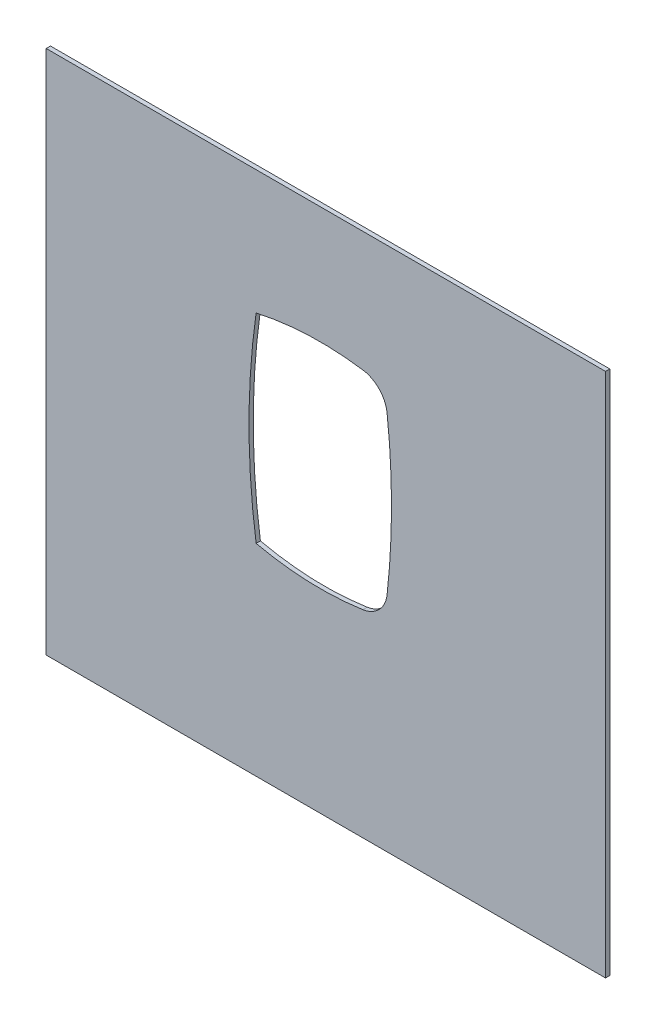
SolidWorks part; units mm, degrees
material "Rostfreier Chromstahl"
ref_plane "Ebene vorne" through (0, 0, 0) normal (0, 0, 1) x (1, 0, 0)
ref_plane "Ebene oben" through (0, 0, 0) normal (0, 1, 0) x (1, 0, 0)
ref_plane "Ebene rechts" through (0, 0, 0) normal (1, 0, 0) x (0, 0, -1)
sketch "Skizze1" plane through (0, 0, 0) normal (0, 0, 1) x (1, 0, 0)
  line L0 (0, -130) -> (0, 130) construction
  line L1 (442.5, 0) -> (-442.5, 0) construction
  line L2 (0, -130) -> (0, 75) construction
  line L4 (-192.2736, 157.0766) -> (200.1363, 157.0766)
  line L5 (-442.5, 0) -> (50, 0) construction
  line L6 (0, 130) -> (0, -75) construction
  line L7 (442.5, 0) -> (-50, 0) construction
  line L8 (-192.2736, 157.0766) -> (-192.2736, -211.5028)
  line L9 (-192.2736, -211.5028) -> (200.1363, -211.5028)
  line L10 (200.1363, 157.0766) -> (200.1363, -211.5028)
  arc A0 (29.9369, 72.8023) -> (-45, 70) centre (0, -130) ccw
  arc A1 (-45, -70) -> (29.9369, -72.8023) centre (0, 130) ccw
  arc A2 (-45, 70) -> (-45, -70) centre (442.5, 0) ccw
  arc A3 (46.8899, -55.2608) -> (46.8899, 55.2608) centre (-442.5, 0) ccw
  arc A6 (29.9369, 72.8023) -> (46.8899, 55.2608) centre (27.0162, 53.0167) cw
  arc A7 (29.9369, -72.8023) -> (46.8899, -55.2608) centre (27.0162, -53.0167) ccw
  point P4 (0, 0)
  point P6 (0, 0)
  point P10 (-45, -70)
  point P15 (-45, 70)
  point P19 (45, 70)
  point P26 (45, -70)
  dimension "D1" = 5
  dimension "D2" = 5
  dimension "D5" = 20
  dimension "D3" = 100
  dimension "D4" = 150
extrude "Aufsatz-Linear austragen1" add sketch "Skizze1" along normal blind 3
